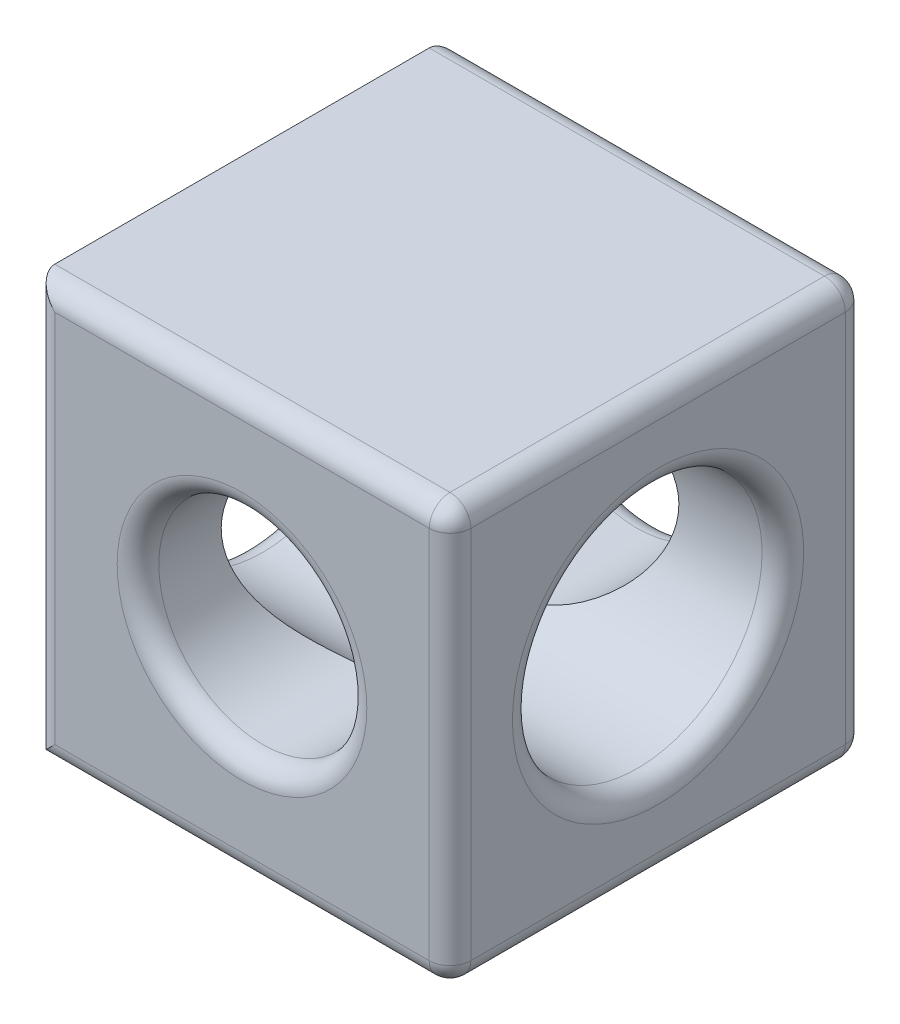
SolidWorks part; units mm, degrees
material "ABS"
ref_plane "前视基准面" through (0, 0, 0) normal (0, 0, 1) x (1, 0, 0)
ref_plane "上视基准面" through (0, 0, 0) normal (0, 1, 0) x (1, 0, 0)
ref_plane "右视基准面" through (0, 0, 0) normal (1, 0, 0) x (0, 0, -1)
other "Configuration Table"
sketch "草图1" plane through (0, 0, 0) normal (0, 0, 1) x (1, 0, 0)
  line L1 (0, 10) -> (10, 10)
  line L2 (0, 10) -> (0, 0)
  line L3 (0, 0) -> (10, 0)
  line L4 (10, 10) -> (10, 0)
  dimension "D1" = 10
  dimension "D2" = 10
extrude "凸台-拉伸1" add sketch "草图1" along normal blind 10
sketch "草图4" plane through (10, 0, 0) normal (1, 0, 0) x (0, 0, -1)
  line L0 (-10, 5) -> (0, 5) construction
  line L1 (-10, 0) -> (-10, 10) construction
  line L2 (0, 0) -> (0, 10) construction
  circle A0 centre (-5, 5) radius 3
  dimension "D1" = 6
  dimension "D2" = 5
extrude "切除-拉伸2" cut sketch "草图4" against normal through all
sketch "草图5" plane through (0, 0, 10) normal (0, 0, 1) x (1, 0, 0)
  line L0 (0, 5) -> (10, 5) construction
  line L1 (0, 10) -> (0, 0) construction
  line L2 (10, 0) -> (10, 10) construction
  circle A0 centre (5, 5) radius 2.5
  dimension "D1" = 5
extrude "切除-拉伸3" cut sketch "草图5" against normal through all
fillet "圆角1" radius 0.5 14 edges at (0, 5, 2) (5, 0, 0) (5, 10, 0) (0, 5, 0) (7.5, 5, 0) (10, 0, 5) (10, 10, 5) (10, 5, 0) (10, 5, 2) (5, 10, 10) (10, 5, 10) (5, 0, 10) (0, 5, 10) (7.5, 5, 10)
